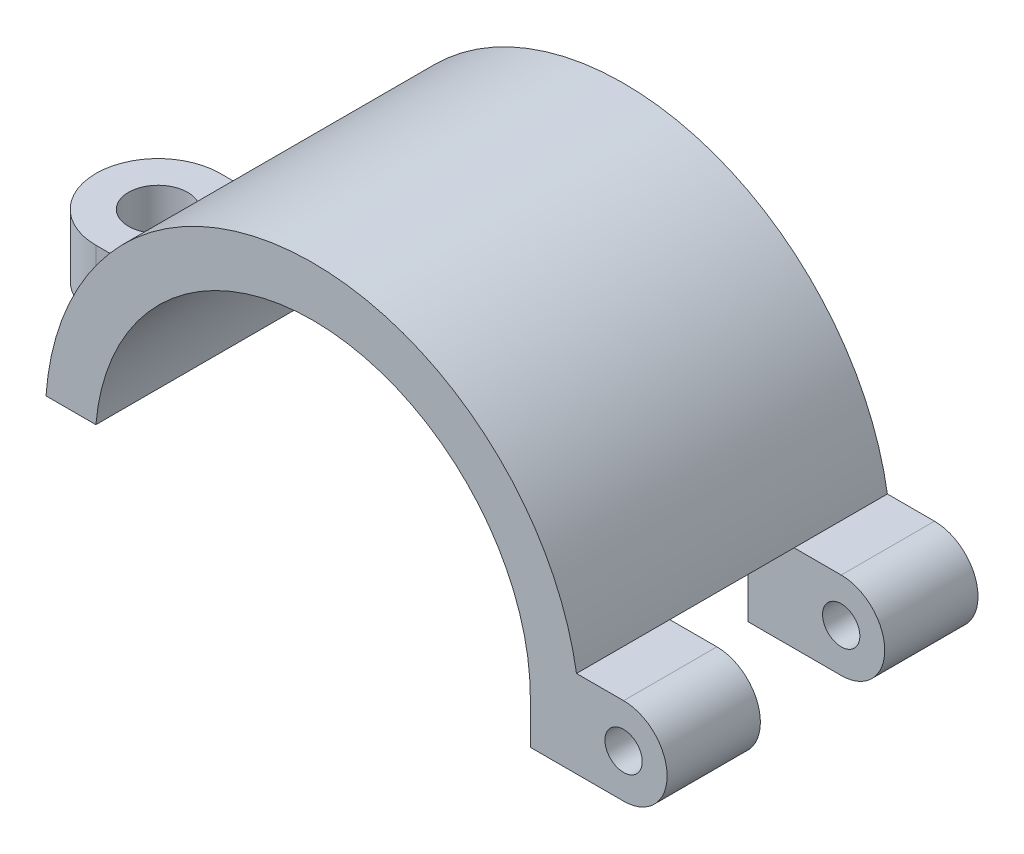
SolidWorks part; units mm, degrees
ref_plane "Plan de face" through (0, 0, 0) normal (0, 0, 1) x (1, 0, 0)
ref_plane "Plan de dessus" through (0, 0, 0) normal (0, 1, 0) x (1, 0, 0)
ref_plane "Plan de droite" through (0, 0, 0) normal (1, 0, 0) x (0, 0, -1)
sketch "Esquisse1" plane through (0, 0, 0) normal (0, 0, 1) x (1, 0, 0)
  line L0 (-17.4356, 1.5) -> (-21.4476, 1.5)
  line L3 (17.5, 0) -> (21.5, 0)
  line L6 (0, 0) -> (0, 2.9531) construction
  arc A0 (-17.4356, 1.5) -> (17.5, 0) centre (0, 0) cw
  arc A1 (-21.4476, 1.5) -> (21.5, 0) centre (0, 0) cw
  dimension "D1" = 17.5
  dimension "D4" = 4
  dimension "D3" = 1.5
extrude "Boss.-Extru.1" add sketch "Esquisse1" along normal blind 25
sketch "Esquisse2" plane through (0, 1.5, 0) normal (0, -1, 0) x (1, 0, 0)
  line L0 (-17.4356, 7.5) -> (-24.9356, 7.5)
  line L1 (-17.4356, 7.5) -> (-17.4356, 17.5)
  line L2 (-17.4356, 17.5) -> (-24.9356, 17.5)
  line L3 (-17.4356, 25) -> (-17.4356, 0) construction
  line L4 (-24.9356, 12.5) -> (-14.975, 12.5) construction
  line L5 (-21.4476, 0) -> (-17.4356, 0) construction
  line L6 (-21.4476, 25) -> (-17.4356, 25) construction
  arc A0 (-24.9356, 7.5) -> (-24.9356, 17.5) centre (-24.9356, 12.5) cw
  circle A1 centre (-24.9356, 12.5) radius 2.375
  dimension "D1" = 4.75
  dimension "D2" = 10
  dimension "D3" = 7.5
extrude "Boss.-Extru.2" add sketch "Esquisse2" against normal blind 5
sketch "Esquisse3" plane through (0, 0, 25) normal (0, 0, 1) x (1, 0, 0)
  line L0 (17.5, -3.5) -> (25, -3.5)
  line L1 (17.5, -3.5) -> (17.5, 3.5)
  line L2 (17.5, 3.5) -> (25, 3.5)
  line L3 (25, 0) -> (17.5, 0) construction
  arc A0 (25, 3.5) -> (25, -3.5) centre (25, 0) cw
  circle A1 centre (25, 0) radius 1.5
  dimension "D1" = 3
  dimension "D2" = 7
  dimension "D3" = 7.5
extrude "Boss.-Extru.3" add sketch "Esquisse3" against normal blind 7.5
sketch "Esquisse4" plane through (0, 0, 0) normal (0, 0, -1) x (-1, 0, 0)
  line L0 (-17.5, -3.5) -> (-25, -3.5)
  line L1 (-17.5, -3.5) -> (-17.5, 3.5)
  line L2 (-17.5, 3.5) -> (-25, 3.5)
  line L3 (-25, 0) -> (9.4232, 0) construction
  arc A0 (-25, -3.5) -> (-25, 3.5) centre (-25, 0) cw
  circle A1 centre (-25, 0) radius 1.5
  point P2 (0, 0)
  dimension "D1" = 3
  dimension "D2" = 7
  dimension "D3" = 7.5
extrude "Boss.-Extru.4" add sketch "Esquisse4" against normal blind 7.5
sketch "Esquisse5" plane through (0, 0, 17.5) normal (0, 0, -1) x (-1, 0, 0)
  line L0 (-25, 3.5) -> (-21.2132, 3.5) construction
  line L1 (-13.8851, -6.5942) -> (-25, -6.5942)
  line L2 (-13.8851, -6.5942) -> (-13.8851, 3.5)
  line L3 (-13.8851, 3.5) -> (-25, 3.5)
  line L4 (-25, -6.5942) -> (-25, 3.5)
  arc A0 (-25, 3.5) -> (-25, -3.5) centre (-25, 0) ccw construction
  point P10 (-17.5, 3.5)
  point P11 (-15.1901, 3.5)
  point P12 (-13.8851, -6.5942)
extrude "Enlèv. mat.-Extru.1" cut sketch "Esquisse5" along normal up to surface (10 mm away) up to face at (21.8808, 0.001, 7.5)
